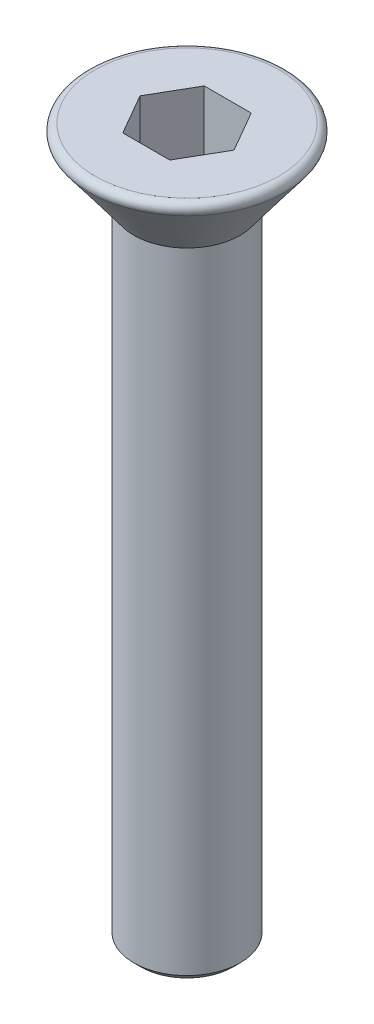
SolidWorks part; units mm, degrees
ref_plane "前视" through (0, 0, 0) normal (0, 0, 1) x (1, 0, 0)
ref_plane "上视" through (0, 0, 0) normal (0, 1, 0) x (1, 0, 0)
ref_plane "右视" through (0, 0, 0) normal (1, 0, 0) x (0, 0, -1)
sketch "草图1" plane through (0, 0, 0) normal (0, 0, 1) x (1, 0, 0)
  line L0 (0, 0) -> (0, -2)
  line L1 (0, -2) -> (1.5, -2)
  line L2 (3, 0) -> (0, 0)
  line L3 (1.5, -2) -> (3, 0)
  dimension "D1" = 3
  dimension "D2" = 1.5
  dimension "D3" = 2
revolve "旋转1" add sketch "草图1" angle 360 about L0
sketch "草图2" plane through (0, -2, 0) normal (0, -1, 0) x (1, 0, 0)
  circle A0 centre (0, 0) radius 1.5
extrude "凸台-拉伸1" add sketch "草图2" along normal blind 18
sketch "草图3" plane through (0, 0, 0) normal (0, 1, 0) x (1, 0, 0)
  line L1 (-1.3279, 0) -> (-0.664, -1.15)
  line L2 (-0.664, -1.15) -> (0.664, -1.15)
  line L3 (0.664, -1.15) -> (1.3279, 0)
  line L4 (1.3279, 0) -> (0.664, 1.15)
  line L5 (0.664, 1.15) -> (-0.664, 1.15)
  line L6 (-0.664, 1.15) -> (-1.3279, 0)
  circle A0 centre (0, 0) radius 1.15 construction
  dimension "D1" = 2.3
extrude "切除-拉伸1" cut sketch "草图3" against normal blind 2
chamfer "倒角1" distance 0.2 angle 45 1 edges at (1.5, -20, 0)
fillet "圆角1" radius 0.2 1 edges at (-3, 0, 0)
